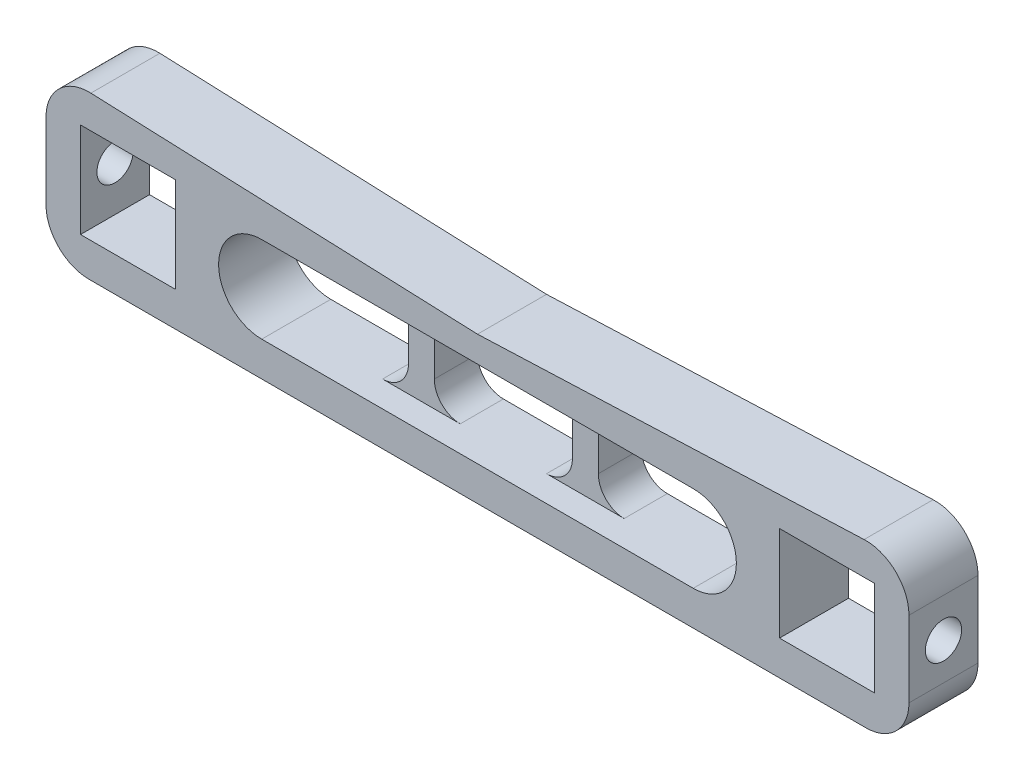
SolidWorks part; units mm, degrees
ref_plane "Front Plane" through (0, 0, 0) normal (0, 0, 1) x (1, 0, 0)
ref_plane "Top Plane" through (0, 0, 0) normal (0, 1, 0) x (1, 0, 0)
ref_plane "Right Plane" through (0, 0, 0) normal (1, 0, 0) x (0, 0, -1)
sketch "Sketch1" plane through (0, 0, 0) normal (0, 0, 1) x (1, 0, 0)
  line L0 (30, 30.4159) -> (30, -18.8897) construction
  line L1 (-46, -4) -> (-35, -4)
  line L2 (-46, -4) -> (-46, -15)
  line L3 (-46, -15) -> (-35, -15)
  line L4 (-35, -4) -> (-35, -15)
  line L5 (35, -4) -> (46, -4)
  line L6 (35, -4) -> (35, -15)
  line L7 (35, -15) -> (46, -15)
  line L8 (46, -4) -> (46, -15)
  line L9 (-30, 24.7677) -> (-30, -19) construction
  line L11 (50, -5.204) -> (50, -14)
  line L12 (45, -19) -> (-45, -19)
  line L13 (-50, -14) -> (-50, -5.204)
  line L14 (-44.8002, -0.208) -> (0, -2)
  line L15 (0, -2) -> (44.8002, -0.208)
  line L16 (0, 32.0731) -> (0, -32.3501) construction
  line L17 (-25, -10) -> (25, -10) construction
  line L18 (-25, -5) -> (25, -5)
  line L19 (-25, -15) -> (25, -15)
  arc A0 (44.8002, -0.208) -> (50, -5.204) centre (45, -5.204) cw
  arc A1 (50, -14) -> (45, -19) centre (45, -14) cw
  arc A2 (-45, -19) -> (-50, -14) centre (-45, -14) cw
  arc A3 (-44.8002, -0.208) -> (-50, -5.204) centre (-45, -5.204) ccw
  arc A4 (-25, -5) -> (-25, -15) centre (-25, -10) ccw
  arc A5 (25, -15) -> (25, -5) centre (25, -10) ccw
  point P20 (0, -10)
  point P23 (50, 0)
  point P30 (-50, 0)
  dimension "D14" = 5
  dimension "D1" = 11
  dimension "D2" = 11
  dimension "D3" = 11
  dimension "D4" = 11
  dimension "D5" = 60
  dimension "D6" = 30
  dimension "D7" = 35
  dimension "D8" = 35
  dimension "D9" = 4
  dimension "D10" = 2
  dimension "D11" = 50
  dimension "D12" = 50
  dimension "D13" = 4
  dimension "D15" = 25
  dimension "D16" = 25
  dimension "D17" = 9
  dimension "D18" = 5
extrude "Boss-Extrude1" add sketch "Sketch1" along normal blind 8
sketch "Sketch2" plane through (0, -5, 0) normal (0, -1, 0) x (1, 0, 0)
  line L0 (0, 0) -> (-44.8002, 0) construction
  line L1 (-11, 0) -> (-8, 0)
  line L2 (-11, 0) -> (-11, 5)
  line L3 (-11, 5) -> (-8, 5)
  line L4 (-8, 0) -> (-8, 5)
  line L5 (44.8002, 0) -> (0, 0) construction
  line L6 (8, 0) -> (11, 0)
  line L7 (8, 0) -> (8, 5)
  line L8 (8, 5) -> (11, 5)
  line L9 (11, 0) -> (11, 5)
  line L10 (0, -16.351) -> (0, 20.8581) construction
  dimension "D1" = 8
  dimension "D2" = 3
  dimension "D3" = 5
extrude "Boss-Extrude2" add sketch "Sketch2" along normal up to next
fillet "Fillet1" radius 3 8 edges at (-11, -15, 2.5) (-11, -5, 2.5) (-8, -15, 2.5) (-8, -5, 2.5) (8, -15, 2.5) (8, -5, 2.5) (11, -15, 2.5) (11, -5, 2.5)
hole_wizard "M5 Tapped Hole1" positions "3DSketch1" profile "Sketch5" tap size "M5" standard "DIN" end condition up to next
sketch3d "3DSketch1"
  line L0 (50, -14, 0) -> (50, -5.204, 0) construction
  line L1 (50, -5.204, 8) -> (50, -5.204, 0) construction
  line L2 (-50, -5.204, 0) -> (-50, -14, 0) construction
  line L3 (-50, -5.204, 8) -> (-50, -5.204, 0) construction
  point P0 (-50, -9.704, 4)
  point P3 (50, -9.704, 4)
  point P10 (0, 0, 0)
  dimension "D1" = 4
  dimension "D2" = 4.5
  dimension "D3" = 4
  dimension "D4" = 4.5
sketch "Sketch5" plane through (-50, -9.704, 4) normal (0, 1, 0) x (0, 0, 1)
  line L0 (0, 0) -> (0, 4)
  line L1 (0, 4) -> (2.1, 4)
  line L2 (2.1, 4) -> (2.1, 0)
  line L5 (2.1, 0) -> (0, 0)
  line L11 (0, -6.35) -> (0, 107.95) construction
  dimension "Thru Tap Drill Dia." = 4.2
  dimension "Thru Tap Drill Depth" = 4
cosmetic thread "Hole Thread1" parameters "D2"=5
cosmetic thread "Hole Thread2" parameters "D2"=5
